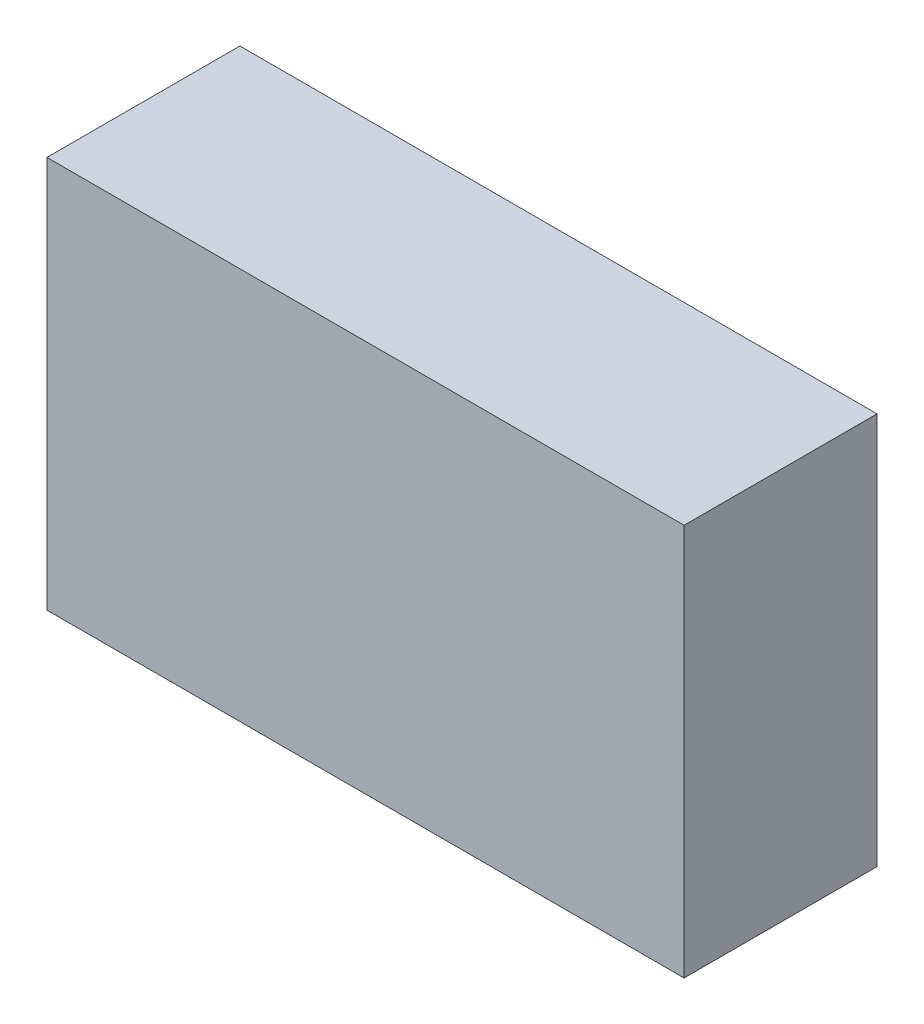
SolidWorks part; units mm, degrees
ref_plane "Front Plane" through (0, 0, 0) normal (0, 0, 1) x (1, 0, 0)
ref_plane "Top Plane" through (0, 0, 0) normal (0, 1, 0) x (1, 0, 0)
ref_plane "Right Plane" through (0, 0, 0) normal (1, 0, 0) x (0, 0, -1)
sketch "Sketch1" plane through (0, 0, 0) normal (0, 0, 1) x (1, 0, 0)
  line L0 (-1.778, 1.016) -> (1.524, 1.016)
  line L1 (1.524, 1.016) -> (1.524, -1.016)
  line L2 (1.524, -1.016) -> (-1.778, -1.016)
  line L3 (-1.778, -1.016) -> (-1.778, 1.016)
extrude "Component_Outline" add sketch "Sketch1" along normal blind 1 separate body
sketch3d "3DSketch1"
  line L0 (0, 0, 0) -> (1, 0, 0)
  line L1 (0, 0, 0) -> (0, 1, 0)
  line L2 (0, 0, 0) -> (0, 0, 1)
  point P0 (0, 0, 0)
